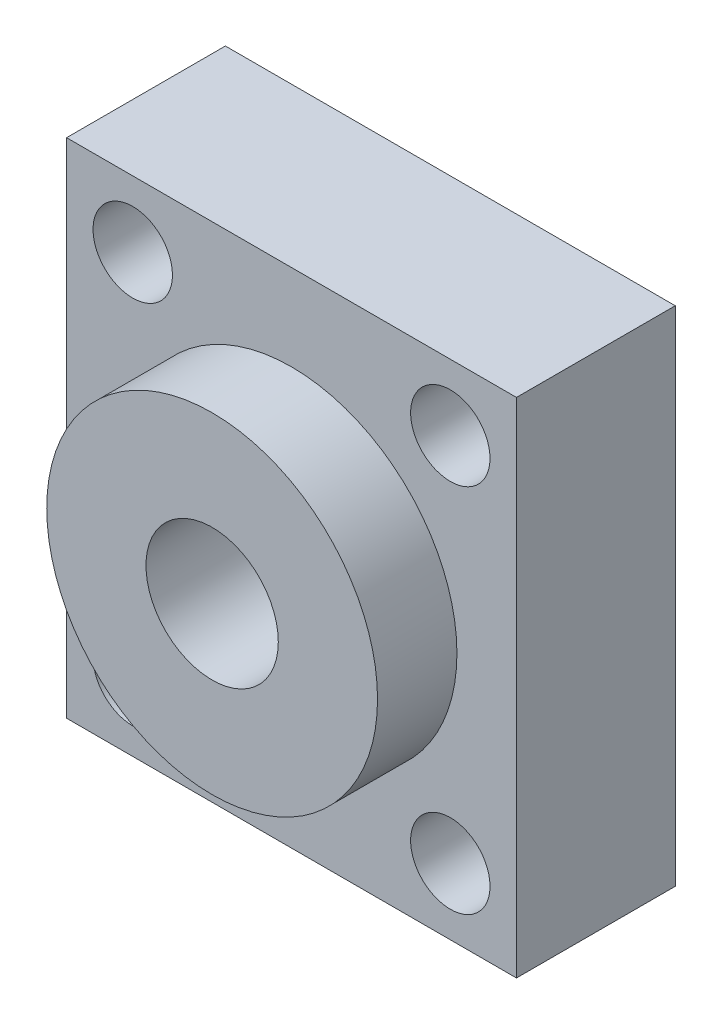
SolidWorks part; units mm, degrees
ref_plane "Front Plane" through (0, 0, 0) normal (0, 0, 1) x (1, 0, 0)
ref_plane "Top Plane" through (0, 0, 0) normal (0, 1, 0) x (1, 0, 0)
ref_plane "Right Plane" through (0, 0, 0) normal (1, 0, 0) x (0, 0, -1)
sketch "Sketch1" plane through (0, 0, 0) normal (0, 0, 1) x (1, 0, 0)
  line L1 (-18.4444, 12.1111) -> (15.5556, 12.1111)
  line L2 (-18.4444, 12.1111) -> (-18.4444, -25.8889)
  line L3 (-18.4444, -25.8889) -> (15.5556, -25.8889)
  line L4 (15.5556, 12.1111) -> (15.5556, -25.8889)
  point P6 (0, 0)
  point P7 (0, 0)
  dimension "D1" = 34
  dimension "D2" = 38
extrude "Boss-Extrude1" add sketch "Sketch1" along normal blind 12
sketch "Эскиз1" plane through (0, 0, 12) normal (0, 0, 1) x (1, 0, 0)
  line L0 (-18.4444, -25.8889) -> (15.5556, -25.8889) construction
  line L1 (15.5556, -25.8889) -> (15.5556, 12.1111) construction
  circle A0 centre (-1.4444, -6.8889) radius 12.5
  dimension "D1" = 19
  dimension "D2" = 17
extrude "Бобышка-Вытянуть1" add sketch "Эскиз1" along normal blind 6
sketch "Эскиз2" plane through (0, 0, 18) normal (0, 0, 1) x (1, 0, 0)
  circle A0 centre (-1.4444, -6.8889) radius 5
  circle A1 centre (-1.4444, -6.8889) radius 12.5 construction
  dimension "D1" = 10
extrude "Вырез-Вытянуть1" cut sketch "Эскиз2" against normal blind 100
sketch "Sketch2" plane through (0, 0, 12) normal (0, 0, 1) x (1, 0, 0)
  line L0 (-18.4444, 12.1111) -> (-18.4444, -25.8889) construction
  line L1 (15.5556, 12.1111) -> (-18.4444, 12.1111) construction
  circle A0 centre (-13.4444, 7.1111) radius 3
  dimension "D1" = 5
  dimension "D2" = 5
extrude "Cut-Extrude1" cut sketch "Sketch2" against normal blind 5
pattern_linear "LPattern1" count 2 spacing 24 along (1, 0, 0) count 2 spacing 28 along (0, -1, 0) of "Cut-Extrude1"
